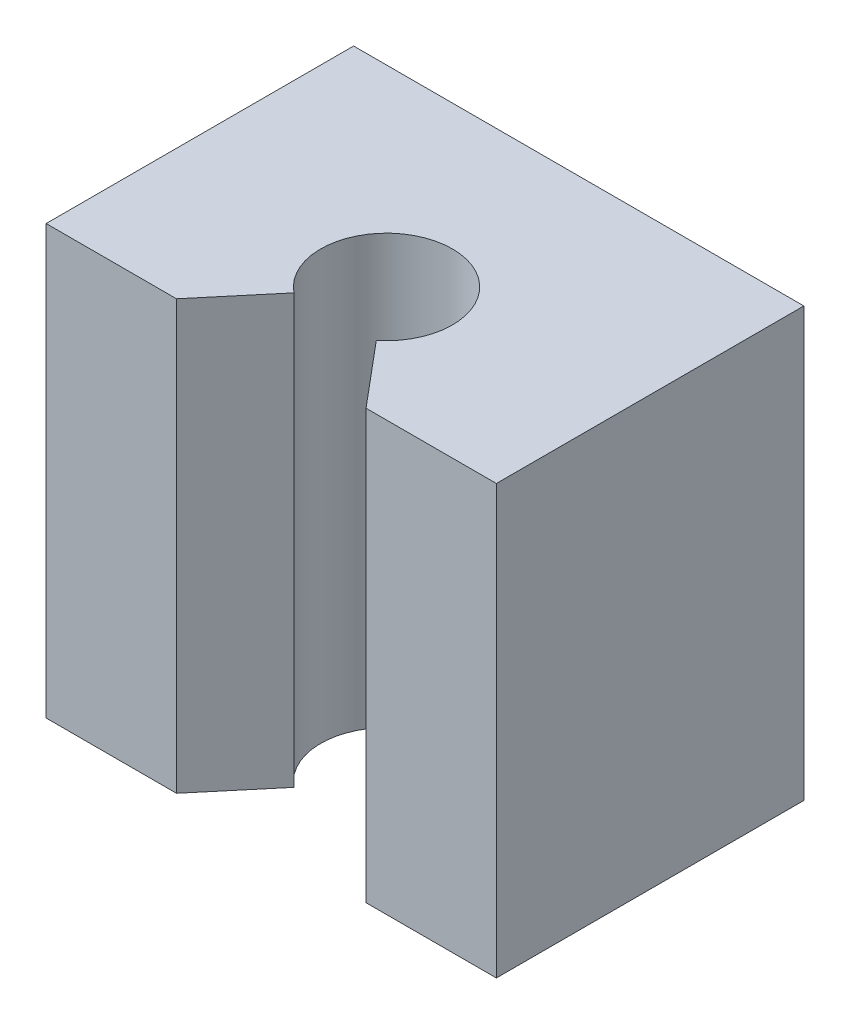
SolidWorks part; units mm, degrees
ref_plane "Front Plane" through (0, 0, 0) normal (0, 0, 1) x (1, 0, 0)
ref_plane "Top Plane" through (0, 0, 0) normal (0, 1, 0) x (1, 0, 0)
ref_plane "Right Plane" through (0, 0, 0) normal (1, 0, 0) x (0, 0, -1)
sketch "Sketch1" plane through (0, 0, 0) normal (0, 1, 0) x (1, 0, 0)
  line L1 (20.5, -10.5) -> (-20.5, -10.5)
  line L2 (20.5, -10.5) -> (20.5, 17.5)
  line L3 (20.5, 17.5) -> (-20.5, 17.5)
  line L4 (-20.5, -10.5) -> (-20.5, 17.5)
  line L5 (20.5, -10.5) -> (-20.5, 17.5) construction
  line L6 (20.5, 17.5) -> (-20.5, -10.5) construction
  circle A0 centre (0, 0) radius 6
  point P3 (0, 3.5)
  point P8 (0, 0)
  dimension "D1" = 12
  dimension "D2" = 28
  dimension "D3" = 41
  dimension "D4" = 17.5
extrude "Boss-Extrude1" add sketch "Sketch1" along normal blind 39
sketch "Sketch2" plane through (0, 39, 0) normal (0, 1, 0) x (1, 0, 0)
  line L0 (0, -1000) -> (0, 49000) construction
  line L1 (-3.75, -4.6837) -> (-17.0214, -20.5)
  line L2 (3.75, -4.6837) -> (17.0214, -20.5)
  line L3 (-24.526, -29.4436) -> (0, -0.2147) construction
  line L4 (24.526, -29.4436) -> (0, -0.2147) construction
  line L5 (-17.0214, -20.5) -> (17.0214, -20.5)
  line L6 (-20.5, -10.5) -> (20.5, -10.5) construction
  circle A0 centre (0, 0) radius 6 construction
  point P0 (-3.75, -4.6837)
  point P1 (3.75, -4.6837)
  point P14 (0, 0)
  dimension "D1" = 7.5
  dimension "D2" = 80
  dimension "D3" = 10
extrude "Cut-Extrude1" cut sketch "Sketch2" against normal through all and the other way through all
sketch "Sketch3" plane through (0, 0, -17.5) normal (0, 0, -1) x (-1, 0, 0)
  line L0 (-20.5, 39) -> (20.5, 0) construction
  line L1 (14, 6.5) -> (-14, 6.5) construction
  line L2 (14, 6.5) -> (14, 32.5) construction
  line L3 (14, 32.5) -> (-14, 32.5) construction
  line L4 (-14, 6.5) -> (-14, 32.5) construction
  line L5 (14, 6.5) -> (-14, 32.5) construction
  line L6 (14, 32.5) -> (-14, 6.5) construction
  circle A0 centre (14, 32.5) radius 2.5
  circle A1 centre (-14, 6.5) radius 2.5
  circle A2 centre (-14, 32.5) radius 2.5
  circle A3 centre (14, 6.5) radius 2.5
  point P0 (0, 19.5)
  point P5 (0, 19.5)
  dimension "D3" = 5
  dimension "D1" = 28
  dimension "D2" = 26
extrude "Cut-Extrude2" cut sketch "Sketch3" against normal blind 10
